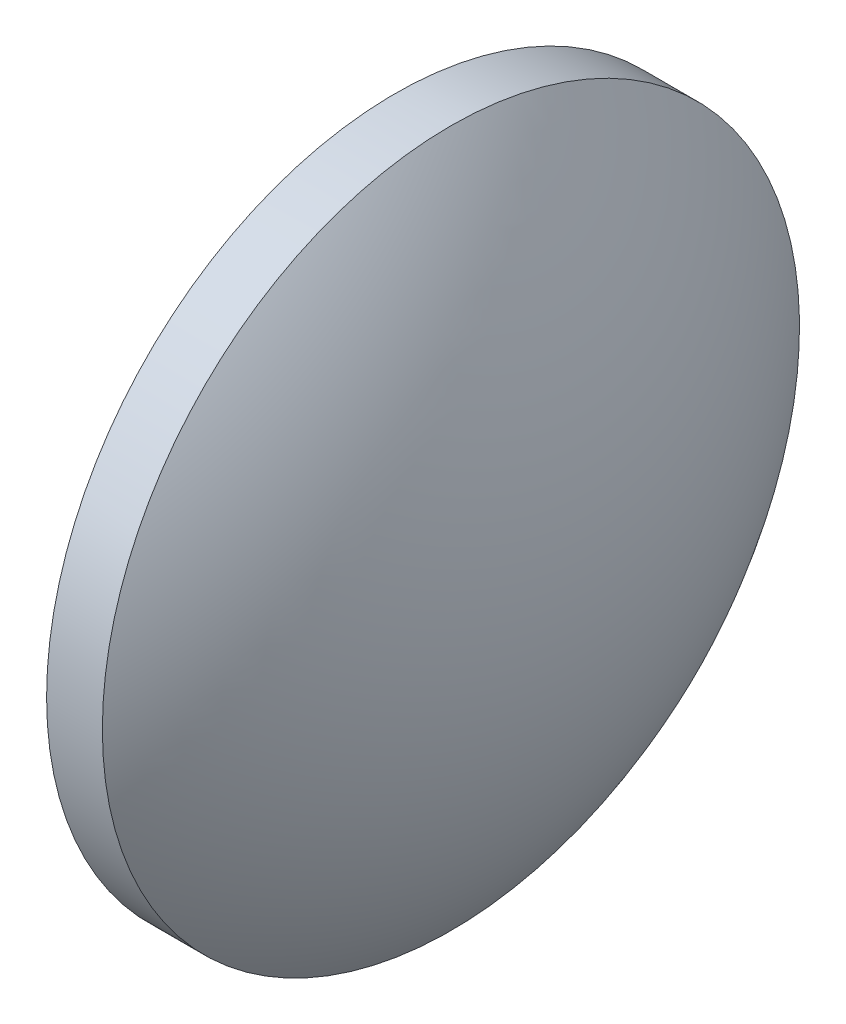
SolidWorks part; units mm, degrees
ref_plane "前视基准面" through (0, 0, 0) normal (0, 0, 1) x (1, 0, 0)
ref_plane "上视基准面" through (0, 0, 0) normal (0, 1, 0) x (1, 0, 0)
ref_plane "右视基准面" through (0, 0, 0) normal (1, 0, 0) x (0, 0, -1)
sketch "草图1" plane through (0, 0, 0) normal (0, 0, 1) x (1, 0, 0)
  line L0 (562.0416, 156.0724) -> (575.4873, 156.0724) construction
  line L1 (563.5536, 156.0724) -> (563.5536, 168.5724)
  line L2 (569.7636, 156.0724) -> (563.5536, 156.0724)
  line L5 (563.5536, 168.5724) -> (565.5536, 168.5724)
  arc A0 (569.7636, 156.0724) -> (565.5536, 168.5724) centre (549.1016, 156.0724) ccw
revolve "旋转1" add sketch "草图1" angle 360 about L0
